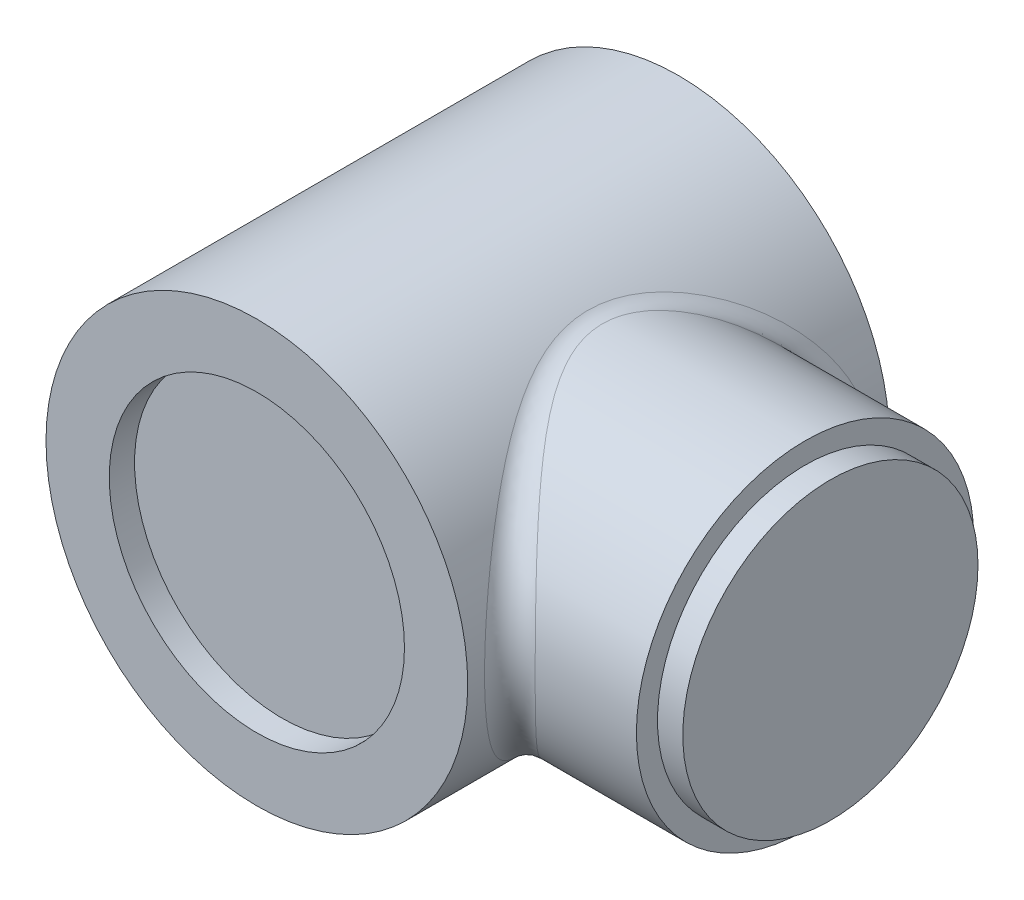
SolidWorks part; units mm, degrees
ref_plane "Front Plane" through (0, 0, 0) normal (0, 0, 1) x (1, 0, 0)
ref_plane "Top Plane" through (0, 0, 0) normal (0, 1, 0) x (1, 0, 0)
ref_plane "Right Plane" through (0, 0, 0) normal (1, 0, 0) x (0, 0, -1)
sketch "Sketch1" plane through (0, 0, 0) normal (0, 0, 1) x (1, 0, 0)
  circle A0 centre (0, 0) radius 25
  dimension "D1" = 50
extrude "Boss-Extrude1" add sketch "Sketch1" along normal mid plane 50
sketch "Sketch2" plane through (0, 0, 25) normal (0, 0, 1) x (1, 0, 0)
  circle A0 centre (0, 0) radius 17.5
  dimension "D1" = 35
extrude "Cut-Extrude1" cut sketch "Sketch2" against normal blind 3
mirror "Mirror1" about plane through (0, 0, 0) normal (0, 0, 1) of "Cut-Extrude1"
sketch "Sketch3" plane through (0, 0, 0) normal (1, 0, 0) x (0, 0, -1)
  circle A0 centre (0, 0) radius 20
  dimension "D1" = 40
extrude "Boss-Extrude2" add sketch "Sketch3" along normal blind 40
sketch "Sketch4" plane through (40, 0, 0) normal (1, 0, 0) x (0, 0, -1)
  circle A0 centre (0, 0) radius 17.5
  dimension "D1" = 35
extrude "Boss-Extrude3" add sketch "Sketch4" along normal blind 3
fillet "Fillet1" radius 3 1 edges at (24.89, 2.3429, -19.8623)
